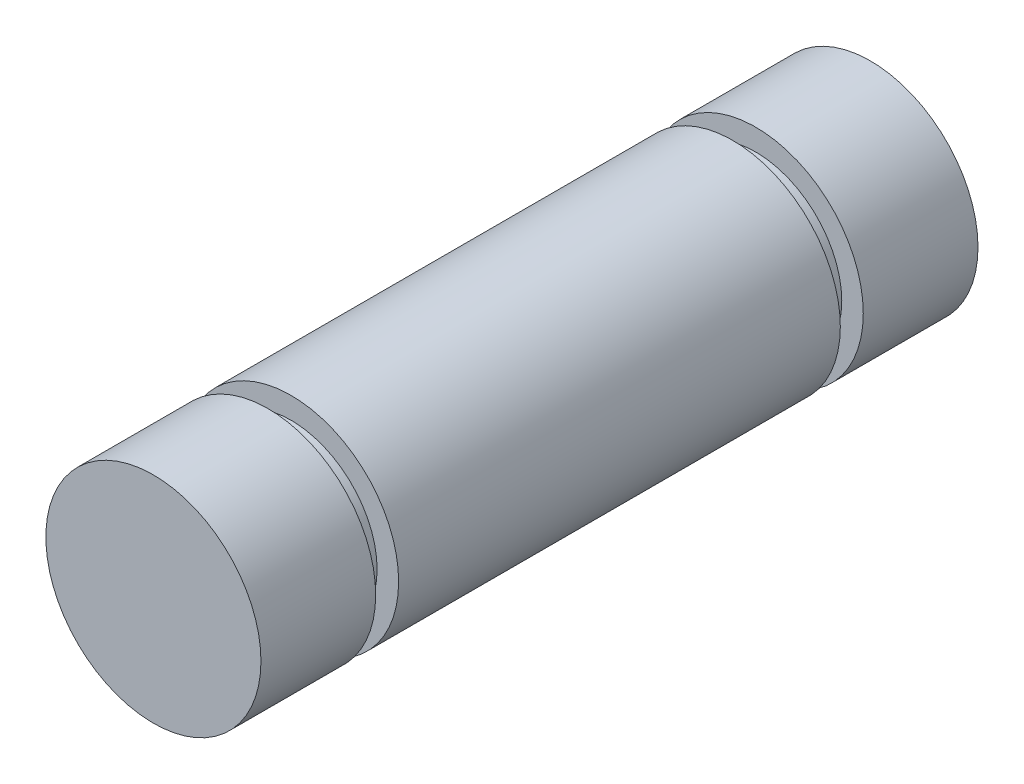
SolidWorks part; units mm, degrees
ref_plane "Front Plane" through (0, 0, 0) normal (0, 0, 1) x (1, 0, 0)
ref_plane "Top Plane" through (0, 0, 0) normal (0, 1, 0) x (1, 0, 0)
ref_plane "Right Plane" through (0, 0, 0) normal (1, 0, 0) x (0, 0, -1)
sketch "Sketch1" plane through (0, 0, 0) normal (0, 0, 1) x (1, 0, 0)
  circle A0 centre (0, 0) radius 4.7625
  dimension "D1" = 9.525
extrude "Boss-Extrude1" add sketch "Sketch1" along normal mid plane 31.75
sketch "Sketch2" plane through (0, 0, 0) normal (0, 1, 0) x (1, 0, 0)
  line L0 (4.7625, -15.875) -> (4.7625, 15.875) construction
  line L1 (4.7625, 10.795) -> (3.81, 10.795)
  line L2 (4.7625, 10.795) -> (4.7625, 9.779)
  line L3 (4.7625, 9.779) -> (3.81, 9.779)
  line L4 (3.81, 10.795) -> (3.81, 9.779)
  line L5 (4.7625, 15.875) -> (-4.7625, 15.875) construction
  line L6 (4.7625, -9.779) -> (3.81, -9.779)
  line L7 (4.7625, -9.779) -> (4.7625, -10.795)
  line L8 (4.7625, -10.795) -> (3.81, -10.795)
  line L9 (3.81, -9.779) -> (3.81, -10.795)
  line L10 (-4.7625, -15.875) -> (4.7625, -15.875) construction
  point P10 (3.81, 10.287)
  dimension "D1" = 0.9525
  dimension "D2" = 0.9525
  dimension "D3" = 1.016
  dimension "D4" = 1.016
  dimension "D5" = 5.08
  dimension "D6" = 5.08
ref_axis "Axis1" through (0, 0, 15.875) along (0, 0, -1)
revolve "Cut-Revolve1" cut sketch "Sketch2" angle 360 about axis through (0, 0, 15.875) along (0, 0, -1)
